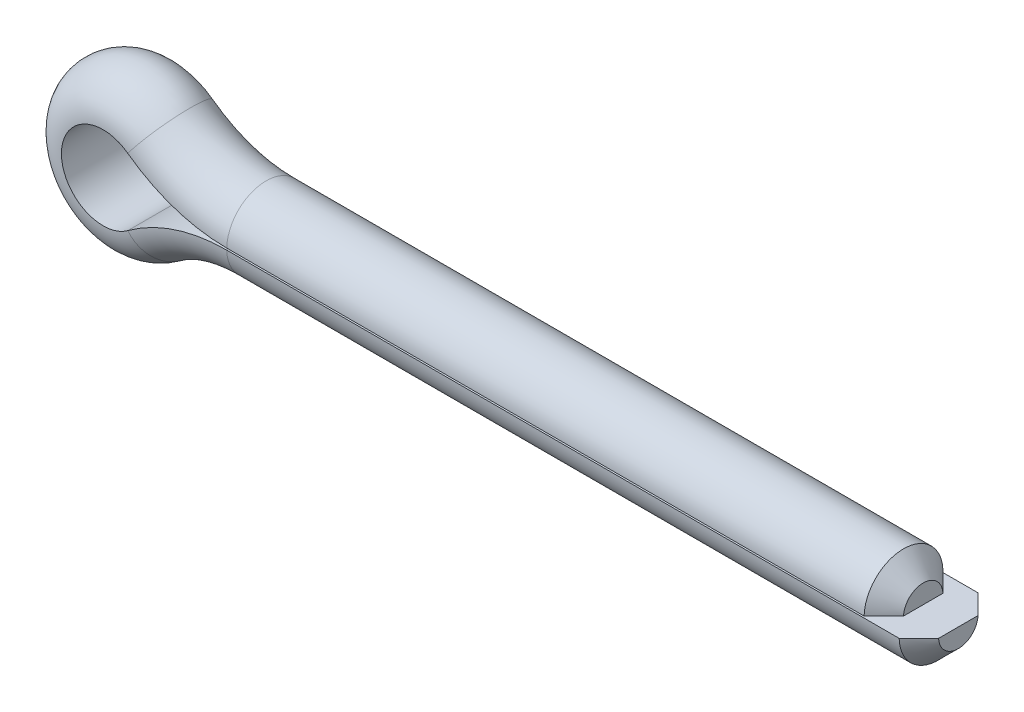
SolidWorks part; units mm, degrees
ref_plane "Front" through (0, 0, 0) normal (0, 0, 1) x (1, 0, 0)
ref_plane "Top" through (0, 0, 0) normal (0, 1, 0) x (1, 0, 0)
ref_plane "Right" through (0, 0, 0) normal (1, 0, 0) x (0, 0, -1)
sketch "Sketch1" plane through (0, 0, 0) normal (0, 0, 1) x (1, 0, 0)
  line L0 (-22.6354, 0) -> (1.016, 0) construction
  line L1 (-19.05, -0.0254) -> (1.016, -0.0254)
  line L2 (-21.4292, 0.0254) -> (1.016, 0.0254) construction
  line L3 (-19.05, 0.0254) -> (0, 0.0254)
  line L4 (-11.4985, 0.0254) -> (1.016, 0.0254) construction
  line L5 (-11.4985, -0.0254) -> (1.016, -0.0254) construction
  line L6 (-22.6354, 1.2065) -> (-22.6354, 0) construction
  line L7 (-22.6354, 1.2065) -> (-22.6354, 2.413) construction
  line L8 (-11.4985, 0) -> (1.016, 0) construction
  line L9 (0, 0.0254) -> (0, 0) construction
  line L10 (-22.6354, 0) -> (-22.6354, -2.413) construction
  line L11 (0, 1.143) -> (0, -1.143) construction
  arc A1 (-21.9183, 0.9703) -> (-21.9183, -0.9703) centre (-22.6354, 0) ccw
  arc A2 (-19.05, -0.0254) -> (-21.9183, -0.9703) centre (-19.05, -4.8514) ccw
  arc A3 (-21.9183, 0.9703) -> (-19.05, 0.0254) centre (-19.05, 4.8514) ccw
  circle A4 centre (-22.6354, 0) radius 2.413 construction
  point P0 (-19.05, 1.143)
  point P15 (0, 0.0254)
  point P25 (0, 0)
  dimension "D6" = 4.826
  dimension "HeadOD" = 4.826
  dimension "ExtendedProngLength" = 1.016
  dimension "Length" = 19.05
  dimension "A" = 2.286
  dimension "D4" = 0.0254
  dimension "D5" = 0.0254
sketch "Sketch2" plane through (0, 0, 0) normal (1, 0, 0) x (0, 0, -1)
  line L0 (-1.143, 0.0254) -> (1.143, 0.0254)
  circle A1 centre (0, 0) radius 1.143 construction
  arc A2 (-1.143, 0.0254) -> (1.143, 0.0254) centre (0, -0.0003) cw
sketch "Sketch3" plane through (0, 0, 0) normal (0, 0, 1) x (1, 0, 0)
  line L0 (-19.05, -0.0254) -> (1.016, -0.0254) construction
  line L1 (-19.05, 0.0254) -> (0, 0.0254) construction
  line L2 (-19.05, -0.0254) -> (1.016, -0.0254)
  line L3 (-19.05, 0.0254) -> (0, 0.0254)
  arc A0 (-19.05, -0.0254) -> (-21.9183, -0.9703) centre (-19.05, -4.8514) ccw construction
  arc A1 (-21.9183, 0.9703) -> (-21.9183, -0.9703) centre (-22.6354, 0) ccw construction
  arc A2 (-21.9183, 0.9703) -> (-19.05, 0.0254) centre (-19.05, 4.8514) ccw construction
  arc A3 (-19.05, -0.0254) -> (-21.9183, -0.9703) centre (-19.05, -4.8514) ccw
  arc A4 (-21.9183, 0.9703) -> (-21.9183, -0.9703) centre (-22.6354, 0) ccw
  arc A5 (-21.9183, 0.9703) -> (-19.05, 0.0254) centre (-19.05, 4.8514) ccw
sketch "Sketch4" plane through (0, 0, 0) normal (1, 0, 0) x (0, 0, -1)
  line L0 (-1.143, 0.0254) -> (1.143, 0.0254) construction
  line L1 (-1.143, 0.0254) -> (1.143, 0.0254)
  arc A2 (1.143, 0.0254) -> (-1.143, 0.0254) centre (0, -0.0003) ccw construction
  arc A3 (1.143, 0.0254) -> (-1.143, 0.0254) centre (0, -0.0003) ccw
sweep "Sweep2" add profiles "Sketch4" path "Sketch3"
chamfer "Chamfer1" distance 0.5715 angle 45 2 edges at (1.016, -1.143, 0) (0, 1.143, 0)
equation "\"D6@Sketch1\" = \"HeadOD@Sketch1\""
equation "\"D1@Chamfer1\" = \"A@Sketch1\" * .25"
equation "\"WireWidth@Sketch2\"=\"A@Sketch1\""
